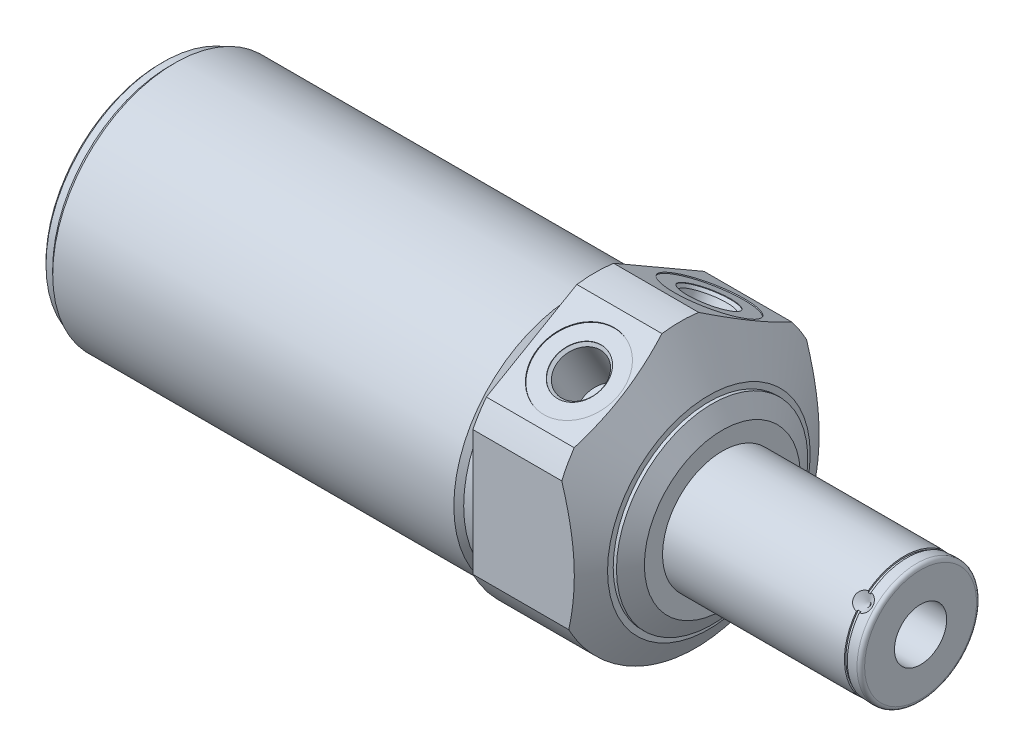
SolidWorks part; units mm, degrees
material "Alloy Steel"
ref_plane "Front Plane" through (0, 0, 0) normal (0, 0, 1) x (1, 0, 0)
ref_plane "Top Plane" through (0, 0, 0) normal (0, 1, 0) x (1, 0, 0)
ref_plane "Right Plane" through (0, 0, 0) normal (1, 0, 0) x (0, 0, -1)
sketch "Sketch1" plane through (0, 0, 0) normal (1, 0, 0) x (0, 0, -1)
  circle A0 centre (0, 0) radius 40
  dimension "D1" = 80
extrude "Extrude1" add sketch "Sketch1" along normal blind 33.7566 and the other way blind 115.4684
sketch "Sketch2" plane through (0, 0, 0) normal (1, 0, 0) x (0, 0, -1)
  line L0 (-14.6964, -3.556) -> (14.6964, -3.556) construction
  circle A0 centre (0, -3.556) radius 32.4231
  circle A1 centre (0, 0) radius 40 construction
  circle A2 centre (0, 0) radius 40
  dimension "D1" = 64.8462
  dimension "D2" = 3.556
extrude "Cut-Extrude1" cut sketch "Sketch2" against normal up to next
sketch "Sketch4" plane through (33.7566, 0, 0) normal (-1, 0, 0) x (0, 0, 1)
  line L0 (32.4993, -16.6421) -> (32.4993, 16.6421)
  line L1 (28.8991, 22.3161) -> (4.8768, 36.1854)
  line L2 (-32.4993, -16.6421) -> (-32.4993, 16.6421)
  line L3 (-28.8991, 22.3161) -> (-4.8768, 36.1854)
  line L4 (0, -20.9029) -> (0, 19.86) construction
  circle A0 centre (0, 0) radius 40 construction
  circle A1 centre (0, 0) radius 40
  arc A2 (-32.4993, -16.6421) -> (32.4993, -16.6421) centre (0, 0) ccw
  arc A3 (32.4993, 16.6421) -> (28.8991, 22.3161) centre (0, 0) ccw
  arc A7 (4.8768, 36.1854) -> (-4.8768, 36.1854) centre (0, 0) ccw
  arc A8 (-28.8991, 22.3161) -> (-32.4993, 16.6421) centre (0, 0) ccw
  dimension "D4" = 73.025
  dimension "D1" = 64.9986
  dimension "D2" = 60
  dimension "D3" = 36.8554
extrude "Cut-Extrude3" cut sketch "Sketch4" along normal up to surface (33.7566 mm away) up to face at (0, -3.556, -32.4231)
sketch "Sketch6" plane through (0, 0, 0) normal (0, 0, 1) x (1, 0, 0)
  line L0 (16.8408, 46.444) -> (30.1752, 23.3482)
  line L1 (1.9872, -3.556) -> (19.8625, -3.556) construction
  line L2 (-115.4684, -3.556) -> (0, -3.556) construction
  line L4 (33.7566, 17.145) -> (33.7566, 46.444)
  line L5 (33.7566, 46.444) -> (16.8408, 46.444)
  line L7 (30.1752, 23.3482) -> (30.1752, 21.844)
  line L8 (30.1752, 21.844) -> (31.0436, 21.844)
  line L9 (31.0436, 21.844) -> (33.7566, 17.145)
  line L11 (33.7566, -16.6421) -> (33.7566, 16.6421) construction
  dimension "D1" = 41.402
  dimension "D2" = 100
  dimension "D3" = 50.8
  dimension "D4" = 3.5814
  dimension "D5" = 30
revolve "Cut-Revolve2" cut sketch "Sketch6" angle 360 about L1
ref_plane "Plane17" through (13.0048, 0, 0) normal (-1, 0, 0) x (0, 0, 1)
sketch "S2D0002" plane through (13.0048, 13.7124, 8.6091) normal (1, 0, 0) x (0, 0.4226, -0.9063)
  line L0 (5.2091, 17.864) -> (9.283, 18.2204)
  line L1 (5.2091, 17.864) -> (5.2202, 17.7374)
  line L2 (5.2202, 17.7374) -> (4.5737, 16.967)
  line L3 (4.5737, 16.967) -> (5.7359, 3.6827)
  line L4 (5.7359, 3.6827) -> (-0.1851, 3.1647)
  line L5 (-0.1851, 3.1647) -> (-1.4425, 17.537)
  line L6 (1.1861, -12.5074) -> (0.0217, 0.8019) construction
  line L7 (9.2608, 18.4734) -> (9.283, 18.2204)
  line L8 (12.8801, 18.7901) -> (-14.7529, 16.3725) construction
  line L9 (9.2608, 18.4734) -> (-1.4425, 17.537)
  dimension "D1" = 21.4884
  dimension "D2" = 0.254
  dimension "D3" = 0.127
  dimension "D4" = 13.3096
  dimension "D5" = 45
  dimension "D6" = 11.8872
  dimension "D7" = 14.1732
  dimension "D8" = 1.27
revolve "Cut-Revolve3" cut sketch "S2D0002" angle 360 about L6
mirror "Mirror1" about plane through (0, 0, 0) normal (0, 0, 1) of "Cut-Revolve3"
sketch "Sketch10" plane through (0, 0, 0) normal (0, 0, 1) x (1, 0, 0)
  line L0 (0, 28.8671) -> (0, 27.559)
  line L1 (0, 27.559) -> (-3.81, 27.559)
  line L2 (-3.81, 27.559) -> (-5.1181, 28.8671)
  line L3 (-5.094, -3.556) -> (0.2426, -3.556) construction
  line L4 (0, 28.8671) -> (-5.1181, 28.8671)
  line L5 (-115.4684, -3.556) -> (0, -3.556) construction
  line L6 (0, 28.8671) -> (-115.4684, 28.8671) construction
  line L7 (0, 16.6421) -> (0, -16.6421) construction
  dimension "D1" = 62.23
  dimension "D2" = 3.81
  dimension "D3" = 45
revolve "Cut-Revolve6" cut sketch "Sketch10" angle 360 about L3
sketch "Sketch12" plane through (0, 0, 0) normal (0, 0, 1) x (1, 0, 0)
  line L0 (-115.4684, 28.8671) -> (-115.4684, 27.559)
  line L1 (-115.4684, 27.559) -> (-112.9284, 27.559)
  line L2 (-112.9284, 27.559) -> (-111.6203, 28.8671)
  line L3 (-50.9283, -3.556) -> (-48.1063, -3.556) construction
  line L4 (-115.4684, 28.8671) -> (-111.6203, 28.8671)
  line L5 (-115.4684, -3.556) -> (-5.1181, -3.556) construction
  line L6 (-5.1181, 28.8671) -> (-115.4684, 28.8671) construction
  line L7 (-115.4684, 28.8671) -> (-115.4684, -35.9791) construction
  dimension "D1" = 62.23
  dimension "D2" = 2.54
  dimension "D3" = 45
revolve "Cut-Revolve8" cut sketch "Sketch12" angle 360 about L3
chamfer "Chamfer1" distance 0.762 angle 45 1 edges at (-115.4684, -3.556, 31.115)
sketch "Sketch13" plane through (0, 0, 0) normal (0, 0, 1) x (1, 0, 0)
  line L0 (33.7566, -3.556) -> (86.386, -3.556)
  line L1 (86.386, -3.556) -> (86.386, -18.415)
  line L2 (85.37, -19.431) -> (33.7566, -19.431)
  line L3 (33.7566, -19.431) -> (33.7566, -3.556)
  line L4 (4.7498, -3.556) -> (27.0459, -3.556) construction
  line L5 (-111.6203, -3.556) -> (-5.1181, -3.556) construction
  line L6 (33.7566, -24.257) -> (33.7566, 17.145) construction
  line L7 (0, 16.6421) -> (0, -16.6421) construction
  arc A0 (85.37, -19.431) -> (86.386, -18.415) centre (85.37, -18.415) ccw
  dimension "D2" = 1.016
  dimension "D1" = 86.386
  dimension "D3" = 31.75
revolve "Revolve1" add sketch "Sketch13" angle 360 about L4
ref_plane "Plane18" through (0, -1.778, -1.778) normal (0, 0.7071, 0.7071) x (-1, 0, 0)
sketch "S2D0001" plane through (0, 0, 0) normal (0, 0, 1) x (1, 0, 0)
  line L0 (86.386, 3.3782) -> (60.986, 3.3782)
  line L1 (60.986, 3.3782) -> (56.8195, -3.556)
  line L2 (86.386, 3.3782) -> (86.386, -3.556)
  line L3 (86.386, -3.556) -> (56.8195, -3.556)
  line L4 (-2.8067, -3.556) -> (-15.8378, -3.556) construction
  line L5 (85.37, -3.556) -> (33.7566, -3.556) construction
  line L6 (86.386, -18.415) -> (86.386, 11.303) construction
  dimension "D1" = 13.8684
  dimension "D2" = 25.4
  dimension "D3" = 59
revolve "Cut-Revolve9" cut sketch "S2D0001" angle 360 about L4
sketch "Sketch16" plane through (0, -6.0705, 2.5145) normal (0, -0.7071, -0.7071) x (1, 0, 0)
  line L0 (82.4236, -19.431) -> (80.0106, -19.431)
  line L1 (80.0106, -19.431) -> (82.4236, -17.018)
  line L2 (82.4236, -19.431) -> (82.4236, -17.018)
  line L3 (82.4236, -3.4788) -> (82.4236, 0.0794) construction
  line L4 (86.386, -18.415) -> (86.386, 11.303) construction
  line L5 (33.7566, -19.431) -> (85.37, -19.431) construction
  dimension "D1" = 3.9624
  dimension "D2" = 4.826
  dimension "D3" = 45
revolve "Cut-Revolve10" cut sketch "Sketch16" angle 360 about L3
pattern_circular "CirPattern1" count 4 over 360 about axis through (4.7498, -3.556, 0) along (-1, 0, 0) of "Cut-Revolve10"
sketch "Sketch21" plane through (0, 0, 0) normal (0, 0, 1) x (1, 0, 0)
  line L1 (82.0426, 12.319) -> (82.8046, 12.319)
  line L2 (82.0426, 12.319) -> (82.0426, 11.938)
  line L3 (82.0426, 11.938) -> (82.8046, 11.938)
  line L4 (82.8046, 12.319) -> (82.8046, 11.938)
  line L5 (82.4236, -0.7782) -> (82.4236, 2.3032) construction
  line L7 (23.8735, -3.556) -> (50.6625, -3.556) construction
  line L10 (86.386, -18.415) -> (86.386, 11.303) construction
  line L11 (94.3526, -3.556) -> (67.4049, -3.556) construction
  dimension "D1" = 0.381
  dimension "D2" = 0.762
  dimension "D3" = 3.5814
  dimension "D4" = 15.875
revolve "Cut-Revolve11" cut sketch "Sketch21" angle 360 about L7
